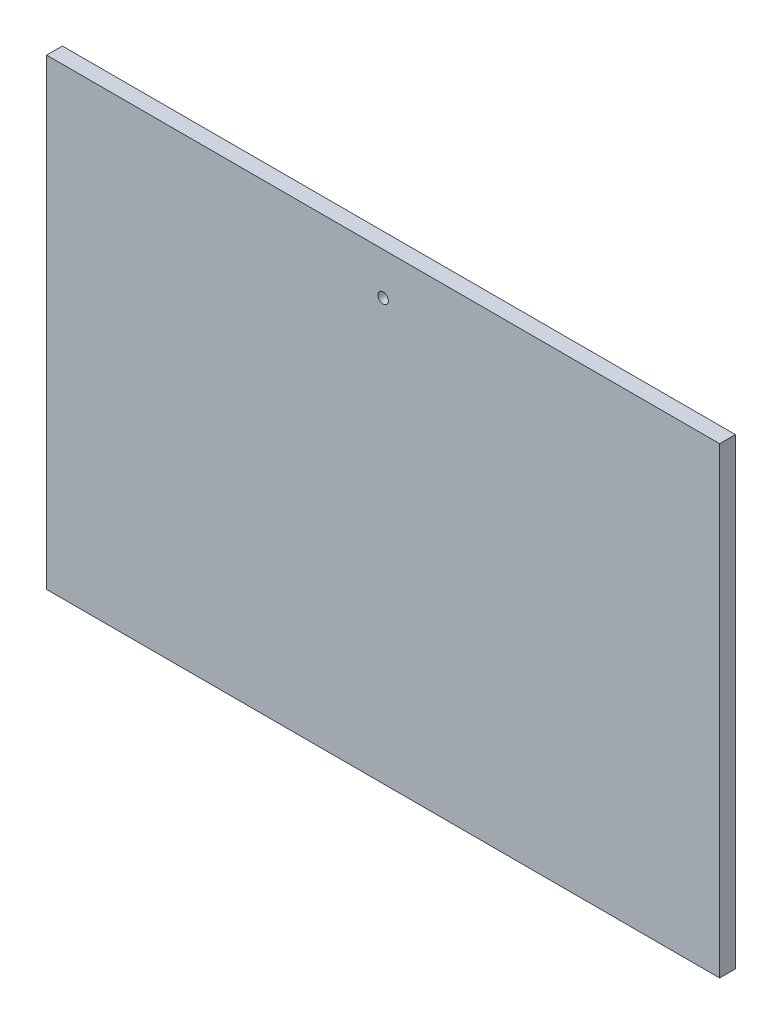
SolidWorks part; units mm, degrees
ref_plane "前视基准面" through (0, 0, 0) normal (0, 0, 1) x (1, 0, 0)
ref_plane "上视基准面" through (0, 0, 0) normal (0, 1, 0) x (1, 0, 0)
ref_plane "右视基准面" through (0, 0, 0) normal (1, 0, 0) x (0, 0, -1)
sketch "草图1" plane through (0, 0, 0) normal (0, 0, 1) x (1, 0, 0)
  line L0 (-59.2182, 38.9328) -> (4.7818, 38.9328)
  line L1 (4.7818, 38.9328) -> (4.7818, -11.0672)
  line L2 (4.7818, -11.0672) -> (-59.2182, -11.0672)
  line L3 (-59.2182, -11.0672) -> (-59.2182, 38.9328)
  line L4 (-27.2182, 38.9328) -> (-27.2182, 31.9328) construction
  circle A0 centre (-27.2182, 31.9328) radius 0.5
extrude "凸台-拉伸1" add sketch "草图1" along normal blind 1.5
sketch "草图2" plane through (0, 0, 1.5) normal (0, 0, 1) x (1, 0, 0)
  line L0 (-59.2182, -11.0672) -> (-59.2182, -8.0672)
  line L1 (-59.2182, 38.9328) -> (-59.2182, -11.0672) construction
  line L2 (-59.2182, -8.0672) -> (4.7818, -8.0672)
  line L3 (4.7818, -11.0672) -> (4.7818, 38.9328) construction
  line L4 (4.7818, -8.0672) -> (4.7818, -11.0672)
  line L5 (4.7818, -11.0672) -> (-59.2182, -11.0672)
  line L6 (-59.2182, 13.9328) -> (11.6606, 13.9328) construction
  line L7 (4.7818, 38.9328) -> (-59.2182, 38.9328)
  line L8 (4.7818, 35.9328) -> (4.7818, 38.9328)
  line L9 (-59.2182, 35.9328) -> (4.7818, 35.9328)
  line L10 (-59.2182, 38.9328) -> (-59.2182, 35.9328)
extrude "切除-拉伸1" cut sketch "草图2" against normal blind 1.5
